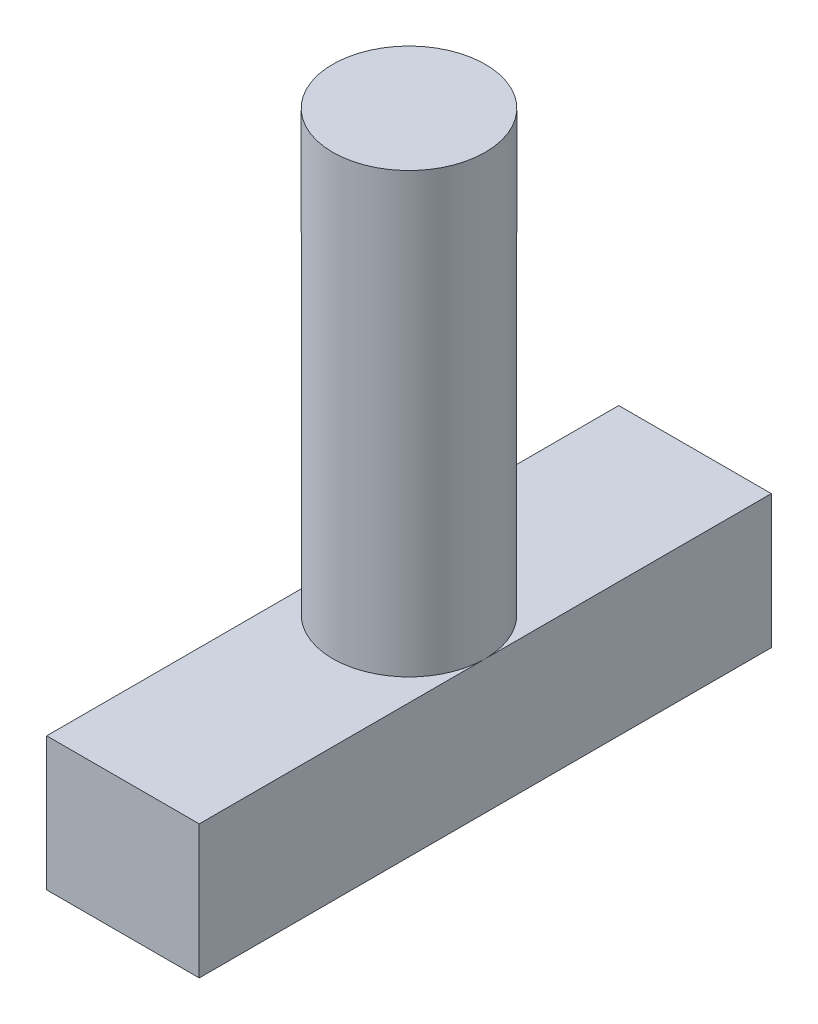
SolidWorks part; units mm, degrees
ref_plane "Alzado" through (0, 0, 0) normal (0, 0, 1) x (1, 0, 0)
ref_plane "Planta" through (0, 0, 0) normal (0, 1, 0) x (1, 0, 0)
ref_plane "Vista lateral" through (0, 0, 0) normal (1, 0, 0) x (0, 0, -1)
sketch "Croquis1" plane through (0, 0, 0) normal (0, 1, 0) x (1, 0, 0)
  circle A0 centre (0, 0) radius 2
  dimension "D1" = 4
extrude "Saliente-Extruir1" add sketch "Croquis1" along normal blind 15
sketch "Croquis2" plane through (0, 0, 0) normal (0, 1, 0) x (1, 0, 0)
  line L1 (2, 7.5) -> (-2, 7.5)
  line L2 (2, 7.5) -> (2, -7.5)
  line L3 (2, -7.5) -> (-2, -7.5)
  line L4 (-2, 7.5) -> (-2, -7.5)
  line L5 (2, 7.5) -> (-2, -7.5) construction
  line L6 (2, -7.5) -> (-2, 7.5) construction
  circle A0 centre (0, 0) radius 2 construction
  point P0 (0, 0)
  dimension "D1" = 15
extrude "Saliente-Extruir2" add sketch "Croquis2" along normal blind 3.5
